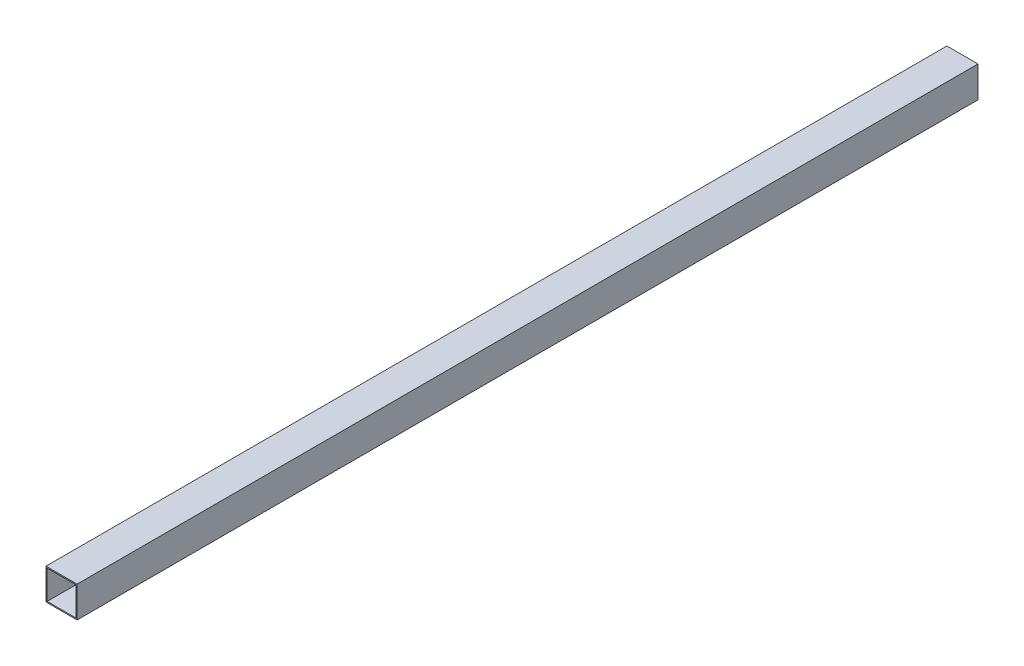
SolidWorks part; units mm, degrees
material "AISI 1020"
ref_plane "Plano frontal" through (0, 0, 0) normal (0, 0, 1) x (1, 0, 0)
ref_plane "Plano superior" through (0, 0, 0) normal (0, 1, 0) x (1, 0, 0)
ref_plane "Plano direito" through (0, 0, 0) normal (1, 0, 0) x (0, 0, -1)
sketch "Esboço1" plane through (0, 0, 0) normal (0, 0, 1) x (1, 0, 0)
  line L1 (-20, -20) -> (20, -20)
  line L2 (-20, -20) -> (-20, 20)
  line L3 (-20, 20) -> (20, 20)
  line L4 (20, -20) -> (20, 20)
  line L5 (-20, -20) -> (20, 20) construction
  line L6 (-20, 20) -> (20, -20) construction
  point P0 (0, 0)
  dimension "D1" = 40
  dimension "D2" = 40
extrude "Ressalto-extrusão1" add sketch "Esboço1" along normal blind 1159
sketch "Esboço2" plane through (0, 0, 1159) normal (0, 0, 1) x (1, 0, 0)
  line L1 (-18.5, -18.5) -> (18.5, -18.5)
  line L2 (-18.5, -18.5) -> (-18.5, 18.5)
  line L3 (-18.5, 18.5) -> (18.5, 18.5)
  line L4 (18.5, -18.5) -> (18.5, 18.5)
  line L5 (-18.5, -18.5) -> (18.5, 18.5) construction
  line L6 (-18.5, 18.5) -> (18.5, -18.5) construction
  point P0 (0, 0)
  dimension "D1" = 37
  dimension "D2" = 37
extrude "Corte-extrusão1" cut sketch "Esboço2" against normal through all
